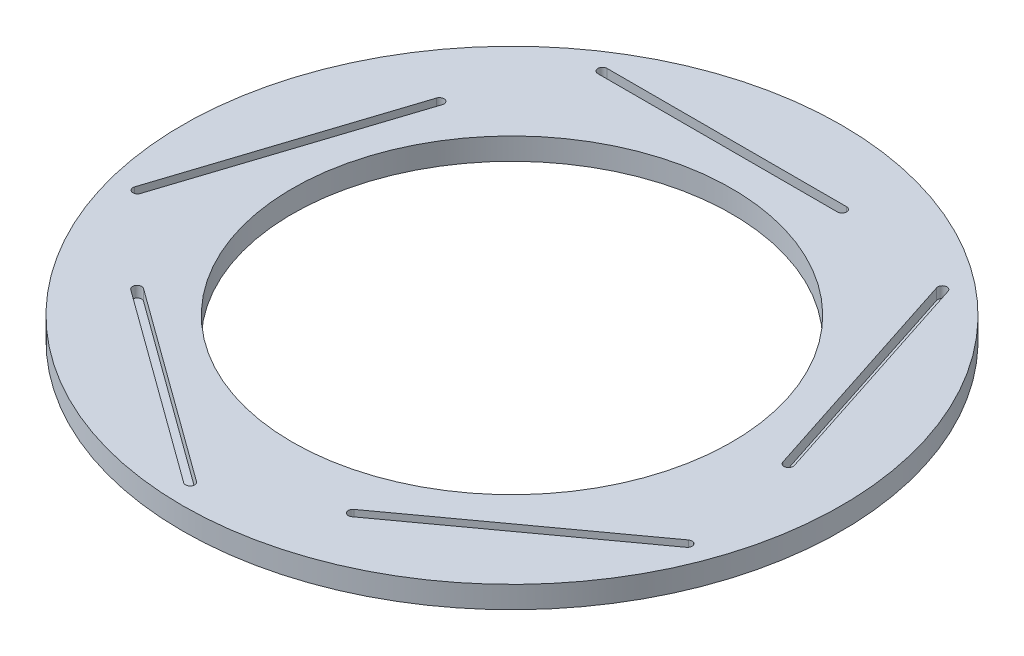
SolidWorks part; units mm, degrees
ref_plane "Front Plane" through (0, 0, 0) normal (0, 0, 1) x (1, 0, 0)
ref_plane "Top Plane" through (0, 0, 0) normal (0, 1, 0) x (1, 0, 0)
ref_plane "Right Plane" through (0, 0, 0) normal (1, 0, 0) x (0, 0, -1)
sketch "Sketch1" plane through (0, 0, 0) normal (0, 1, 0) x (1, 0, 0)
  circle A0 centre (0, 0) radius 45
  circle A1 centre (0, 0) radius 30
extrude "Boss-Extrude1" add sketch "Sketch1" along normal blind 3
sketch "Sketch2" plane through (0, 3, 0) normal (0, 1, 0) x (1, 0, 0)
  line L0 (0, 0) -> (0, 35.0632)
  line L4 (10, 35.0632) -> (-22.714, 35.0632) construction
  line L5 (10, 34.4382) -> (-22.714, 34.4382)
  line L6 (10, 35.6882) -> (-22.714, 35.6882)
  arc A2 (10, 34.4382) -> (10, 35.6882) centre (10, 35.0632) ccw
  arc A3 (-22.714, 35.6882) -> (-22.714, 34.4382) centre (-22.714, 35.0632) ccw
  point P10 (-6.357, 35.0632)
extrude "Cut-Extrude1" cut sketch "Sketch2" against normal blind 1.5
pattern_circular "CirPattern1" count 5 over 360 about axis through (0, 0, 0) along (0, 1, 0) of "Cut-Extrude1"
